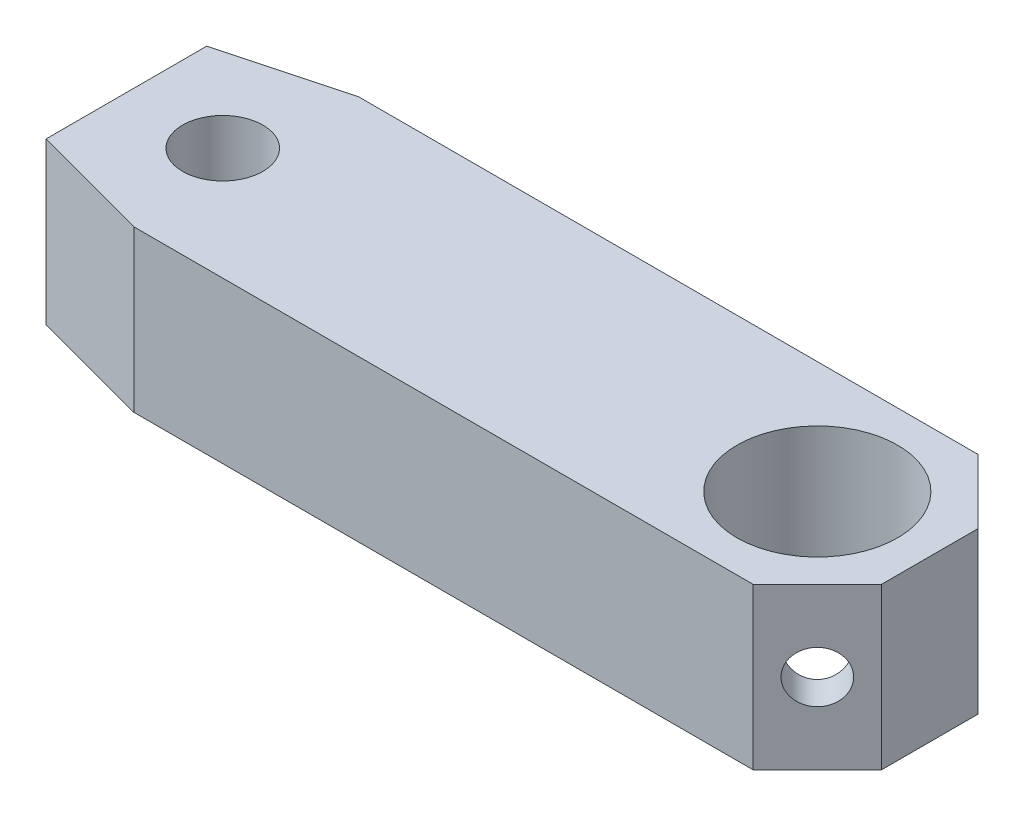
SolidWorks part; units mm, degrees
ref_plane "Front Plane" through (0, 0, 0) normal (0, 0, 1) x (1, 0, 0)
ref_plane "Top Plane" through (0, 0, 0) normal (0, 1, 0) x (1, 0, 0)
ref_plane "Right Plane" through (0, 0, 0) normal (1, 0, 0) x (0, 0, -1)
sketch "block" plane through (0, 0, 0) normal (0, 1, 0) x (1, 0, 0)
  line L0 (18.5, 0) -> (22, 3.5) construction
  line L1 (0.7321, 3.5) -> (20, 3.5)
  line L2 (-3, 2.5) -> (-3, -2.5)
  line L3 (0.7321, -3.5) -> (20, -3.5)
  line L4 (22, 1.5) -> (22, -1.5)
  line L5 (-3, 3.5) -> (22, -3.5) construction
  line L6 (-3, -3.5) -> (22, 3.5) construction
  line L7 (20, 3.5) -> (22, 1.5)
  line L8 (-3, -2.5) -> (0.7321, -3.5)
  line L9 (0.7321, 3.5) -> (-3, 2.5)
  line L10 (20, -3.5) -> (22, -1.5)
  circle A0 centre (18.5, 0) radius 2.5
  point P0 (0, 0)
  point P4 (9.5, 0)
  point P11 (21, 2.5)
  point P21 (21, -2.5)
  dimension "D2" = 5
  dimension "D1" = 18.5
  dimension "D3" = 0
  dimension "D4" = 0
  dimension "D5" = 3
  dimension "D6" = 3.5
  dimension "D7" = 3.5
  dimension "D8" = 29.358
  dimension "D9" = 2
  dimension "D10" = 45
  dimension "D11" = 1
  dimension "D12" = 75
  dimension "D13" = 1
  dimension "D14" = 75
  dimension "D15" = 2
  dimension "D16" = 45
extrude "Boss-Extrude1" add sketch "block" against normal blind 5 contours L1 L9 L2 L8 L3 L4 L7 A0
hole_wizard "M3 Tapped Hole1" positions "Sketch4" profile "Sketch5" tap size "M3" standard "ISO"
sketch "Sketch4" plane through (0, 0, 0) normal (0, 1, 0) x (1, 0, 0)
  line L0 (0, -55) -> (0, 55) construction
  line L1 (-55, 0) -> (55, 0) construction
  point P0 (0, 0)
  dimension "D1" = 0
  dimension "D2" = 0
sketch "Sketch5" plane through (0, 0, 0) normal (1, 0, 0) x (0, 0, 1)
  line L0 (0, 0) -> (0, 5)
  line L1 (0, 5) -> (1.25, 5)
  line L2 (1.25, 5) -> (1.25, 0)
  line L5 (1.25, 0) -> (0, 0)
  line L11 (0, -6.35) -> (0, 107.95) construction
  dimension "Thru Tap Drill Dia." = 2.5
  dimension "Thru Tap Drill Depth" = 5
cosmetic thread "Hole Thread1"
hole_wizard "M2 Tapped Hole1" positions "Sketch8" profile "Sketch9" tap size "M2" standard "ISO"
sketch "Sketch8" plane through (11.75, 0, -11.75) normal (0.7071, 0, -0.7071) x (-0.7071, 0, -0.7071)
  line L0 (-13.0815, 0) -> (-13.0815, -5) construction
  line L1 (-11.6673, 0) -> (-14.4957, 0) construction
  line L2 (-11.6673, -5) -> (-14.4957, -5) construction
  line L3 (-13.0815, -5) -> (-13.0815, -2.5) construction
  line L4 (-13.0815, -2.5) -> (-14.4957, -2.5) construction
  line L5 (-14.4957, -5) -> (-14.4957, 0) construction
  point P0 (-13.0815, -2.5)
  dimension "D1" = 0
  dimension "D2" = 0
sketch "Sketch9" plane through (21, -2.5, -2.5) normal (0, 1, 0) x (-0.7071, 0, -0.7071)
  line L0 (0, 0) -> (0, 1.0355)
  line L1 (0, 1.0355) -> (0.8, 1.0355)
  line L2 (0.8, 1.0355) -> (0.8, 0)
  line L5 (0.8, 0) -> (0, 0)
  line L11 (0, -6.35) -> (0, 107.95) construction
  dimension "Thru Tap Drill Dia." = 1.6
  dimension "Thru Tap Drill Depth" = 1.0355
cosmetic thread "Hole Thread3"
mirror "Mirror1" about plane through (0, 0, 0) normal (0, 0, 1)
cosmetic thread "Hole Thread4"
equation "\"D6@block\" = \"D2@block\" / 2 + 1"
equation "\"D7@block\" = \"D2@block\" / 2 + 1"
equation "\"D1@block\"=\"D2@block\"/2+16mm"
